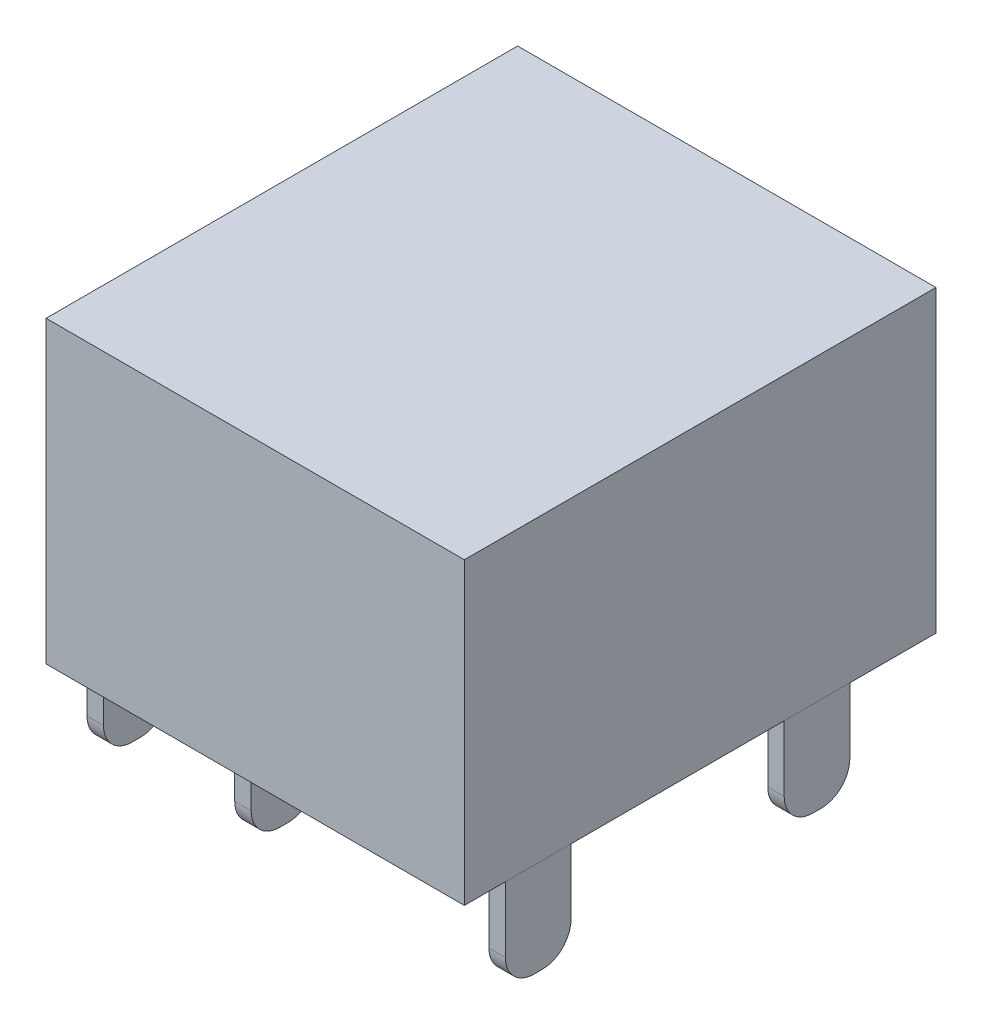
SolidWorks part; units mm, degrees
ref_plane "Front" through (0, 0, 0) normal (0, 0, 1) x (1, 0, 0)
ref_plane "Top" through (0, 0, 0) normal (0, 1, 0) x (1, 0, 0)
ref_plane "Right" through (0, 0, 0) normal (1, 0, 0) x (0, 0, -1)
sketch "Эскиз1" plane through (0, 0, 0) normal (1, 0, 0) x (0, 0, -1)
  line L1 (0, 0) -> (11.5, 0)
  line L2 (0, 0) -> (0, 7.3)
  line L3 (0, 7.3) -> (11.5, 7.3)
  line L4 (11.5, 0) -> (11.5, 7.3)
  dimension "D1" = 11.5
  dimension "D2" = 7.3
extrude "Бобышка-Вытянуть1" add sketch "Эскиз1" along normal blind 10.2
sketch "Эскиз2" plane through (0, 0, -11.5) normal (0, 0, -1) x (-1, 0, 0)
  line L0 (-10.2, 3.65) -> (0, 3.65) construction
  line L1 (-10.2, 0) -> (-10.2, 7.3) construction
  line L2 (0, 0) -> (0, 7.3) construction
  circle A0 centre (-4, 3.65) radius 3
  circle A1 centre (-4, 3.65) radius 1.25
  dimension "D1" = 6
  dimension "D2" = 4
  dimension "D3" = 2.5
extrude "Вырез-Вытянуть1" cut sketch "Эскиз2" against normal blind 8.3
fillet "Скругление1" radius 1.12 1 edges at (4, 4.9, -11.5)
sketch "Эскиз3" plane through (0, 0, 0) normal (0, -1, 0) x (1, 0, 0)
  line L0 (5.1, 0) -> (5.1, -11.5) construction
  line L3 (10.2, 0) -> (0, 0) construction
  line L4 (10.2, -11.5) -> (0, -11.5) construction
  line L5 (0, 0) -> (0, -11.5) construction
  line L6 (0, -2.6) -> (0.4, -2.6)
  line L7 (0, -2.6) -> (0, -1)
  line L8 (0, -1) -> (0.4, -1)
  line L9 (0.4, -2.6) -> (0.4, -1)
  line L10 (0, -9.4) -> (0.4, -9.4)
  line L11 (0, -9.4) -> (0, -7.8)
  line L12 (0, -7.8) -> (0.4, -7.8)
  line L13 (0.4, -9.4) -> (0.4, -7.8)
  line L14 (9.8, -9.4) -> (9.8, -7.8)
  line L15 (10.2, -7.8) -> (9.8, -7.8)
  line L16 (10.2, -9.4) -> (10.2, -7.8)
  line L17 (10.2, -9.4) -> (9.8, -9.4)
  line L18 (9.8, -2.6) -> (9.8, -1)
  line L19 (10.2, -1) -> (9.8, -1)
  line L20 (10.2, -2.6) -> (10.2, -1)
  line L21 (10.2, -2.6) -> (9.8, -2.6)
  line L22 (3.6, 0) -> (3.6, -11.5) construction
  line L23 (3.6, -2.6) -> (4, -2.6)
  line L24 (3.6, -2.6) -> (3.6, -1)
  line L25 (3.6, -1) -> (4, -1)
  line L26 (4, -2.6) -> (4, -1)
  dimension "D1" = 0.4
  dimension "D2" = 1.6
  dimension "D3" = 1
  dimension "D4" = 0.4
  dimension "D5" = 1.6
  dimension "D6" = 2.1
  dimension "D7" = 3.2
  dimension "D8" = 0.4
  dimension "D9" = 1.6
extrude "Бобышка-Вытянуть2" add sketch "Эскиз3" along normal blind 2.3 separate body
fillet "Скругление2" radius 0.7 2 edges at (0.2, -2.3, -1) (0.2, -2.3, -2.6)
fillet "Скругление3" radius 0.7 2 edges at (3.8, -2.3, -2.6) (3.8, -2.3, -1)
fillet "Скругление4" radius 0.7 2 edges at (10, -2.3, -2.6) (10, -2.3, -1)
fillet "Скругление5" radius 0.7 2 edges at (0.2, -2.3, -9.4) (0.2, -2.3, -7.8)
fillet "Скругление6" radius 0.7 2 edges at (10, -2.3, -9.4) (10, -2.3, -7.8)
sketch "Эскиз4" plane through (0, 0, 0) normal (0, -1, 0) x (1, 0, 0)
  line L0 (10.2, -11.5) -> (0, -11.5) construction
  line L1 (3, -8.2) -> (4.7, -8.2)
  line L2 (3, -8.2) -> (3, -6.5)
  line L3 (3, -6.5) -> (4.7, -6.5)
  line L4 (4.7, -8.2) -> (4.7, -6.5)
  line L5 (0, 0) -> (0, -11.5) construction
  dimension "D1" = 1.7
  dimension "D2" = 3.3
  dimension "D3" = 3
extrude "Бобышка-Вытянуть3" add sketch "Эскиз4" along normal blind 1.2
fillet "Скругление7" radius 0.2 4 edges at (3, -0.6, -8.2) (4.7, -0.6, -8.2) (4.7, -0.6, -6.5) (3, -0.6, -6.5)
fillet "Скругление8" radius 0.2 1 edges at (4, 6.65, -11.5)
equation "\"D2@Эскиз2\"=\"D1@Эскиз2\"/2+1"
